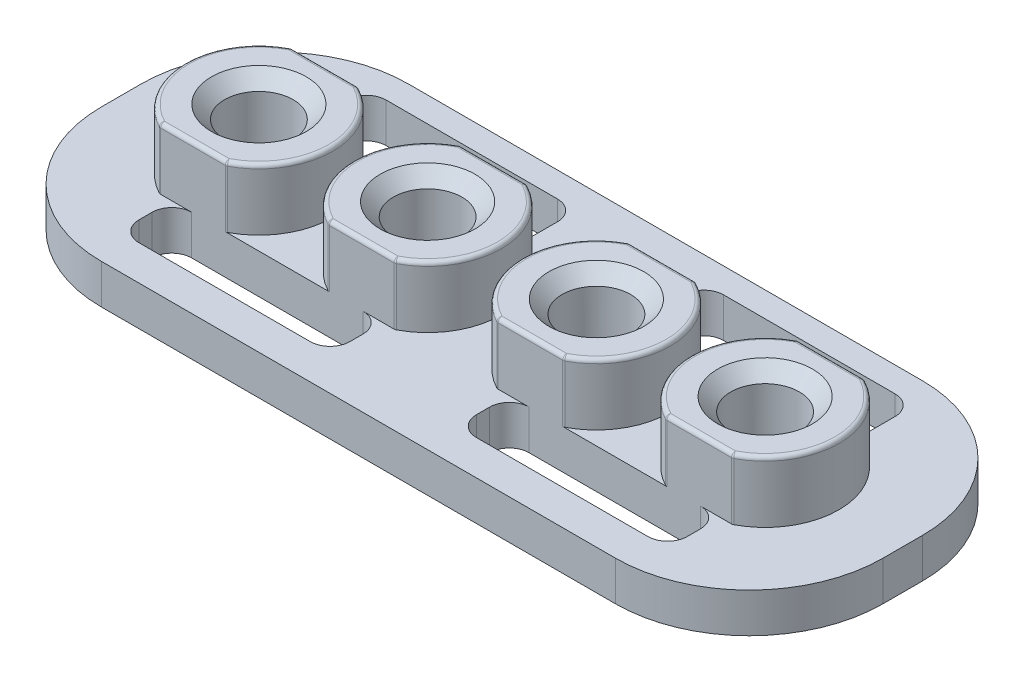
SolidWorks part; units mm, degrees
ref_plane "Front" through (0, 0, 0) normal (0, 0, 1) x (1, 0, 0)
ref_plane "Top" through (0, 0, 0) normal (0, 1, 0) x (1, 0, 0)
ref_plane "Right" through (0, 0, 0) normal (1, 0, 0) x (0, 0, -1)
sketch "Sketch1" plane through (0, 0, 0) normal (0, 1, 0) x (1, 0, 0)
  line L0 (7.5298, -2.9591) -> (-7.5298, 2.9591) construction
  line L1 (-7.5298, 2.9591) -> (7.5298, 2.9591)
  line L2 (-7.5298, 2.9591) -> (-7.5298, -2.9591)
  line L3 (-7.5298, -2.9591) -> (7.5298, -2.9591)
  line L4 (7.5298, 2.9591) -> (7.5298, -2.9591)
  dimension "D1" = 15.0597
  dimension "D2" = 5.9182
extrude "Boss-Extrude1" add sketch "Sketch1" along normal blind 0.762
fillet "Fillet1" radius 2.5781 4 edges at (-7.5298, 0.381, -2.9591) (-7.5298, 0.381, 2.9591) (7.5298, 0.381, -2.9591) (7.5298, 0.381, 2.9591)
sketch "Sketch2" plane through (0, 0.762, 0) normal (0, 1, 0) x (1, 0, 0)
  line L0 (0, 0) -> (0, -4.6727) construction
  line L1 (-50, 0) -> (50, 0) construction
  circle A0 centre (-4.8768, 0) radius 1.4224
  circle A1 centre (-1.6256, 0) radius 1.4224
  circle A2 centre (1.6256, 0) radius 1.4224
  circle A3 centre (4.8768, 0) radius 1.4224
  dimension "D1" = 3.2512
  dimension "D2" = 3.2512
  dimension "D3" = 2.8448
extrude "Boss-Extrude2" add sketch "Sketch2" along normal blind 1.1811
sketch "Sketch3" plane through (0, 1.9431, 0) normal (0, 1, 0) x (1, 0, 0)
  line L0 (0, 0) -> (-8.4412, 0) construction
  line L1 (7.5298, 1.27) -> (-7.5298, 1.27)
  line L2 (7.5298, 1.27) -> (7.5298, 5.8693)
  line L3 (7.5298, 5.8693) -> (-7.5298, 5.8693)
  line L4 (-7.5298, 1.27) -> (-7.5298, 5.8693)
  line L5 (-7.5298, -1.27) -> (-7.5298, -5.8693)
  line L6 (7.5298, -5.8693) -> (-7.5298, -5.8693)
  line L7 (7.5298, -1.27) -> (7.5298, -5.8693)
  line L8 (7.5298, -1.27) -> (-7.5298, -1.27)
  line L9 (-7.5298, 0.381) -> (-7.5298, -0.381) construction
  line L10 (7.5298, -0.381) -> (7.5298, 0.381) construction
  dimension "D1" = 2.54
extrude "Cut-Extrude1" cut sketch "Sketch3" against normal up to surface (1.1811 mm away) up to face at (1.6256, 0.762, -1.4224)
sketch "Sketch4" plane through (0, 1.9431, 0) normal (0, 1, 0) x (1, 0, 0)
  circle A0 centre (-4.8768, 0) radius 0.6604
  circle A1 centre (-1.6256, 0) radius 0.6604
  circle A2 centre (1.6256, 0) radius 0.6604
  circle A3 centre (4.8768, 0) radius 0.6604
  dimension "D1" = 1.3208
extrude "Cut-Extrude2" cut sketch "Sketch4" against normal blind 1.397
sketch "Sketch5" plane through (0, 0.762, 0) normal (0, 1, 0) x (1, 0, 0)
  line L0 (-4.2362, 1.27) -> (-5.5174, 1.27) construction
  line L1 (-5.2832, 2.4765) -> (-1.2192, 2.4765)
  line L2 (-5.2832, 2.4765) -> (-5.2832, 1.27)
  line L3 (-5.2832, 1.27) -> (-1.2192, 1.27)
  line L4 (-1.2192, 2.4765) -> (-1.2192, 1.27)
  line L5 (-5.2832, -1.27) -> (-1.2192, -1.27)
  line L6 (-5.2832, -1.27) -> (-5.2832, -2.286)
  line L7 (-5.2832, -2.286) -> (-1.2192, -2.286)
  line L8 (-1.2192, -1.27) -> (-1.2192, -2.286)
  line L9 (-4.2362, -1.27) -> (-5.5174, -1.27) construction
  line L10 (0, 0) -> (0, -3.7275) construction
  line L11 (1.2192, -1.27) -> (1.2192, -2.286)
  line L12 (5.2832, -2.286) -> (1.2192, -2.286)
  line L13 (5.2832, -1.27) -> (5.2832, -2.286)
  line L14 (5.2832, -1.27) -> (1.2192, -1.27)
  line L15 (1.2192, 2.4765) -> (1.2192, 1.27)
  line L16 (5.2832, 1.27) -> (1.2192, 1.27)
  line L17 (5.2832, 2.4765) -> (5.2832, 1.27)
  line L18 (5.2832, 2.4765) -> (1.2192, 2.4765)
  dimension "D1" = 4.064
  dimension "D2" = 1.2065
  dimension "D3" = 4.064
  dimension "D4" = 1.016
  dimension "D5" = 2.4384
  dimension "D6" = 2.4384
extrude "Cut-Extrude3" cut sketch "Sketch5" against normal through all
fillet "Fillet2" radius 0.381 16 edges at (5.2832, 0.381, -1.27) (5.2832, 0.381, -2.4765) (1.2192, 0.381, -2.4765) (1.2192, 0.381, -1.27) (-1.2192, 0.381, -1.27) (-1.2192, 0.381, -2.4765) (-5.2832, 0.381, -2.4765) (-5.2832, 0.381, -1.27) (-5.2832, 0.381, 2.286) (-1.2192, 0.381, 2.286) (1.2192, 0.381, 2.286) (5.2832, 0.381, 2.286) (5.2832, 0.381, 1.27) (1.2192, 0.381, 1.27) (-1.2192, 0.381, 1.27) (-5.2832, 0.381, 1.27)
chamfer "Chamfer1" distance 0.254 angle 45 4 edges at (-4.8768, 1.9431, 0.6604) (-1.6256, 1.9431, 0.6604) (4.8768, 1.9431, 0.6604) (1.6256, 1.9431, 0.6604)
fillet "Fillet3" radius 0.127 4 edges at (1.6256, 0.5461, 0.6604) (-4.8768, 0.5461, 0.6604) (-1.6256, 0.5461, 0.6604) (4.8768, 0.5461, 0.6604)
fillet "Fillet4" radius 0.0762 32 edges at (-0.2032, 1.9431, 0) (-3.048, 1.9431, 0) (-1.6256, 1.9431, 1.27) (-1.6256, 1.9431, -1.27) (-2.2662, 1.3526, -1.27) (-0.985, 1.3526, -1.27) (-4.2362, 1.3526, -1.27) (-5.5174, 1.3526, -1.27) (-3.4544, 1.9431, 0) (-6.2992, 1.9431, 0) (-4.8768, 1.9431, -1.27) (-4.8768, 1.9431, 1.27) (-4.2362, 1.3526, 1.27) (-5.5174, 1.3526, 1.27) (-2.2662, 1.3526, 1.27) (-0.985, 1.3526, 1.27) (0.985, 1.3526, 1.27) (2.2662, 1.3526, 1.27) (4.2362, 1.3526, 1.27) (5.5174, 1.3526, 1.27) (3.4544, 1.9431, 0) (6.2992, 1.9431, 0) (4.8768, 1.9431, 1.27) (4.2362, 1.3526, -1.27) (5.5174, 1.3526, -1.27) (4.8768, 1.9431, -1.27) (1.6256, 1.9431, 1.27) (0.2032, 1.9431, 0) (3.048, 1.9431, 0) (0.985, 1.3526, -1.27) (2.2662, 1.3526, -1.27) (1.6256, 1.9431, -1.27)
sketch "Sketch6" plane through (0, 0.5461, 0) normal (0, 1, 0) x (1, 0, 0)
  circle A0 centre (-1.6256, 0) radius 0.8509
  dimension "D1" = 1.7018
